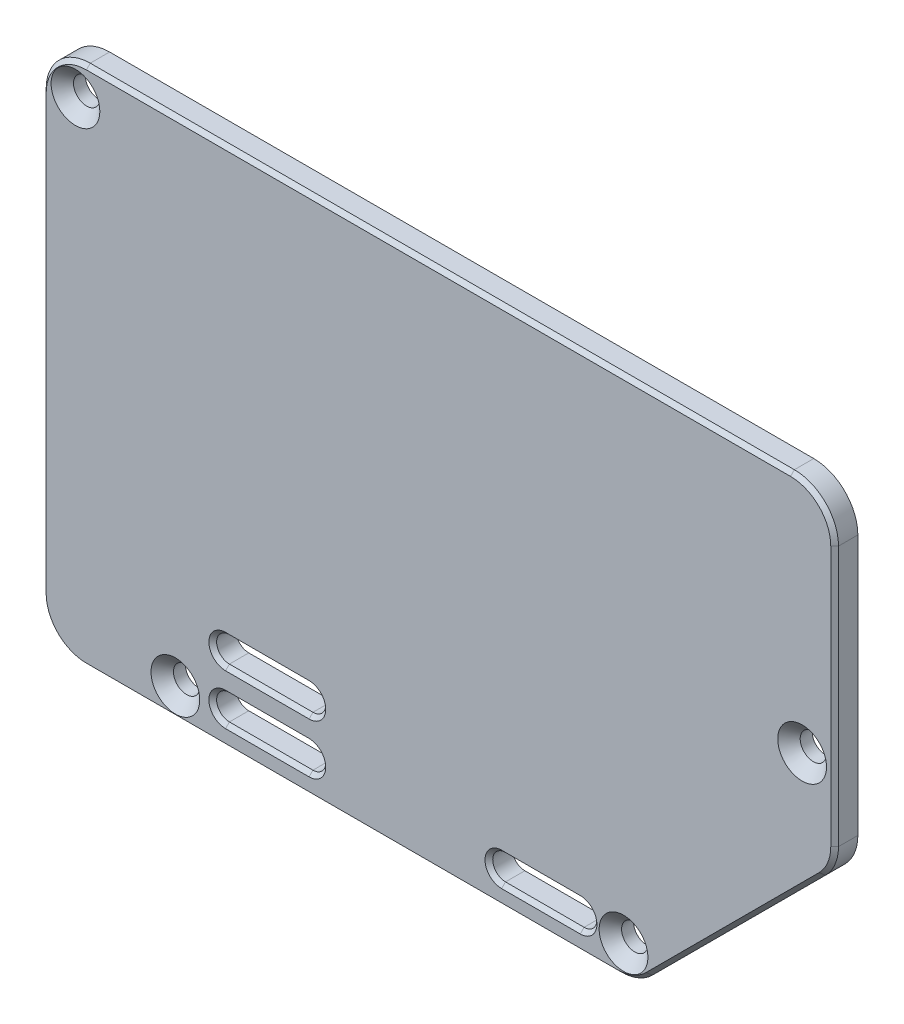
SolidWorks part; units mm, degrees
ref_plane "Front Plane" through (0, 0, 0) normal (0, 0, 1) x (1, 0, 0)
ref_plane "Top Plane" through (0, 0, 0) normal (0, 1, 0) x (1, 0, 0)
ref_plane "Right Plane" through (0, 0, 0) normal (1, 0, 0) x (0, 0, -1)
sketch "Sketch2" plane through (0, 0, 8.62) normal (0, 0, 1) x (1, 0, 0)
  line L0 (4.5, 66.2) -> (95.5, 66.2)
  line L1 (101.2, 60.5) -> (101.2, 26.864)
  line L2 (99.5305, 22.8335) -> (77.1665, 0.4695)
  line L3 (73.136, -1.2) -> (4.5, -1.2)
  line L4 (-1.2, 4.5) -> (-1.2, 60.5)
  line L5 (-1.5, 60.5) -> (-1.5, 4.5) construction
  arc A0 (4.5, -1.2) -> (-1.2, 4.5) centre (4.5, 4.5) cw
  arc A1 (77.1665, 0.4695) -> (73.136, -1.2) centre (73.136, 4.5) cw
  arc A2 (101.2, 26.864) -> (99.5305, 22.8335) centre (95.5, 26.864) cw
  arc A3 (95.5, 66.2) -> (101.2, 60.5) centre (95.5, 60.5) cw
  arc A4 (4.5, 66.2) -> (-1.2, 60.5) centre (4.5, 60.5) ccw
  arc A5 (-1.5, 4.5) -> (4.5, -1.5) centre (4.5, 4.5) ccw construction
  arc A6 (4.5, 66.5) -> (-1.5, 60.5) centre (4.5, 60.5) ccw construction
  arc A7 (101.5, 60.5) -> (95.5, 66.5) centre (95.5, 60.5) ccw construction
  arc A8 (73.136, -1.5) -> (77.3787, 0.2574) centre (73.136, 4.5) ccw construction
  circle A9 centre (3.0858, 61.9142) radius 1.5 construction
  circle A10 centre (16, 2.5) radius 1.5 construction
  circle A11 centre (73.9175, 2.659) radius 1.5 construction
  circle A12 centre (97, 35.5) radius 1.5 construction
  arc A14 (101.3205, 25.4074) -> (101.5, 26.864) centre (95.5, 26.864) ccw construction
  dimension "D1" = 0.3
  dimension "D2" = 3
extrude "Boss-Extrude1" add sketch "Sketch2" along normal blind 3
hole_wizard "CSK for M3 Flat Head Machine Screw1" positions "Sketch4" profile "Sketch5" countersink size "M3" standard "ANSI Metric" end condition through all
sketch "Sketch4" plane through (0, 0, 11.62) normal (0, 0, 1) x (1, 0, 0)
  point P0 (3.0858, 61.9142)
  point P3 (16, 2.5)
  point P6 (73.9175, 2.659)
  point P9 (97, 35.5)
sketch "Sketch5" plane through (3.0858, 61.9142, 11.62) normal (1, 0, 0) x (0, -1, 0)
  line L0 (0, 0) -> (0, 3)
  line L1 (0, 3) -> (1.7, 3)
  line L2 (1.7, 3) -> (1.7, 1.45)
  line L3 (1.7, 1.45) -> (3.15, 0)
  line L5 (3.15, 0) -> (0, 0)
  line L6 (-1.7, 1.45) -> (-3.15, 0) construction
  line L11 (0, -6.35) -> (0, 107.95) construction
  dimension "Thru Hole Dia." = 3.4
  dimension "Thru Hole Depth" = 3
  dimension "Near C'Sink Dia." = 6.3
  dimension "Near C'Sink Angle" = 90
sketch "Sketch6" plane through (0, 0, 11.62) normal (0, 0, 1) x (1, 0, 0)
  line L0 (33.278, 9.5885) -> (22.483, 9.5885) construction
  line L1 (33.278, 7.9375) -> (22.483, 7.9375)
  line L2 (33.278, 11.2395) -> (22.483, 11.2395)
  line L3 (33.278, 3.1115) -> (22.483, 3.1115) construction
  line L4 (33.278, 1.4605) -> (22.483, 1.4605)
  line L5 (33.278, 4.7625) -> (22.483, 4.7625)
  line L6 (27.8805, 11.85) -> (27.8805, 9.5885) construction
  line L8 (34.3805, 11.85) -> (21.3805, 11.85) construction
  line L10 (68.326, 3.048) -> (58.166, 3.048) construction
  line L11 (68.326, 1.397) -> (58.166, 1.397)
  line L12 (68.326, 4.699) -> (58.166, 4.699)
  line L13 (27.8805, 3.1115) -> (27.8805, 0.85) construction
  line L14 (21.3805, 0.85) -> (34.3805, 0.85) construction
  arc A0 (33.278, 7.9375) -> (33.278, 11.2395) centre (33.278, 9.5885) ccw
  arc A1 (22.483, 11.2395) -> (22.483, 7.9375) centre (22.483, 9.5885) ccw
  arc A2 (33.278, 1.4605) -> (33.278, 4.7625) centre (33.278, 3.1115) ccw
  arc A3 (22.483, 4.7625) -> (22.483, 1.4605) centre (22.483, 3.1115) ccw
  arc A4 (68.326, 1.397) -> (68.326, 4.699) centre (68.326, 3.048) ccw
  arc A5 (58.166, 4.699) -> (58.166, 1.397) centre (58.166, 3.048) ccw
  point P2 (27.8805, 9.5885)
  point P7 (27.8805, 3.1115)
  point P26 (63.246, 3.048)
  dimension "D1" = 3.302
  dimension "D2" = 3.175
  dimension "D3" = 10.795
  dimension "D4" = 3.302
extrude "Cut-Extrude1" cut sketch "Sketch6" against normal through all
sketch "Sketch7" plane through (0, 0, 11.62) normal (0, 0, 1) x (1, 0, 0)
  line L1 (20.6317, 56.5089) -> (68.6317, 56.5089)
  line L2 (19.9967, 55.8739) -> (19.9967, 19.4739)
  line L3 (20.6317, 18.8389) -> (68.6317, 18.8389)
  line L4 (69.2667, 55.8739) -> (69.2667, 19.4739)
  arc A4 (68.6317, 56.5089) -> (69.2667, 55.8739) centre (68.6317, 55.8739) cw
  arc A5 (68.6317, 18.8389) -> (69.2667, 19.4739) centre (68.6317, 19.4739) ccw
  arc A6 (19.9967, 19.4739) -> (20.6317, 18.8389) centre (20.6317, 19.4739) ccw
  arc A7 (20.6317, 56.5089) -> (19.9967, 55.8739) centre (20.6317, 55.8739) ccw
  dimension "D2" = 0.635
split line "Split Line1" [suppressed]
chamfer "Chamfer1" distance 0.5 angle 45 22 edges at (63.246, 1.397, 11.62) (69.977, 3.048, 11.62) (56.515, 3.048, 11.62) (63.246, 4.699, 11.62) (27.8805, 1.4605, 11.62) (34.929, 3.1115, 11.62) (20.832, 3.1115, 11.62) (27.8805, 4.7625, 11.62) (27.8805, 7.9375, 11.62) (34.929, 9.5885, 11.62) (20.832, 9.5885, 11.62) (27.8805, 11.2395, 11.62) (100.7661, 24.6827, 11.62) (101.2, 43.682, 11.62) (88.3485, 11.6515, 11.62) (99.5305, 64.5305, 11.62) (75.3173, -0.7661, 11.62) (50, 66.2, 11.62) (38.818, -1.2, 11.62) (0.4695, 64.5305, 11.62) (0.4695, 0.4695, 11.62) (-1.2, 32.5, 11.62)
